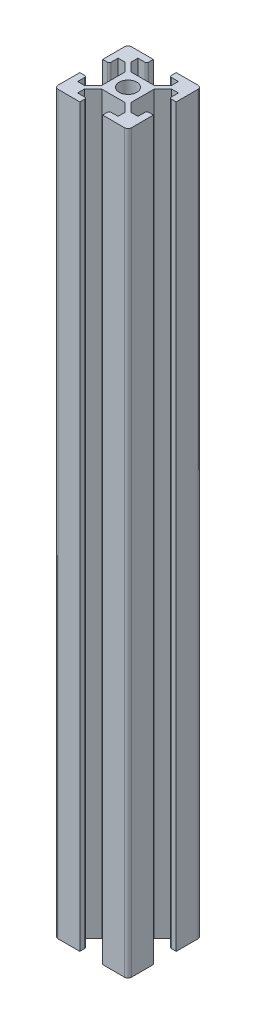
SolidWorks part; units mm, degrees
material "6063-T1"
ref_plane "Front Plane" through (0, 0, 0) normal (0, 0, 1) x (1, 0, 0)
ref_plane "Top Plane" through (0, 0, 0) normal (0, 1, 0) x (1, 0, 0)
ref_plane "Right Plane" through (0, 0, 0) normal (1, 0, 0) x (0, 0, -1)
sketch "Sketch1" plane through (0, 0, 0) normal (0, 1, 0) x (1, 0, 0)
  line L0 (0, 14.3976) -> (0, -18.4644) construction
  line L1 (-9, -10) -> (9, -10)
  line L2 (-10, -9) -> (-10, 9)
  line L3 (-9, 10) -> (9, 10)
  line L4 (10, -9) -> (10, 9)
  line L5 (-15.9976, 0) -> (13.6764, 0) construction
  line L6 (3.1, 10) -> (3.1, 8.2) construction
  line L7 (3.1, 8.2) -> (5.5, 8.2) construction
  line L8 (8.2, 5.5) -> (6.3765, 5.5) construction
  line L9 (3.1235, 4) -> (0, 4) construction
  line L10 (10, 3.1) -> (8.2, 3.1) construction
  line L11 (8.2, 3.1) -> (8.2, 5.5) construction
  line L12 (5.5, 8.2) -> (5.5, 6.3765) construction
  line L13 (4, 3.1235) -> (4, 0) construction
  line L14 (6.3765, 5.5) -> (4, 3.1235) construction
  line L15 (3.1, 10) -> (3.1, 8.7)
  line L16 (5.5, 6.3765) -> (3.1235, 4) construction
  line L17 (3.6, 8.2) -> (5.5, 8.2)
  line L18 (5.5, 8.2) -> (5.5, 6.3765)
  line L19 (5.5, 6.3765) -> (3.1235, 4)
  line L20 (3.1235, 4) -> (0, 4)
  line L21 (10, 3.1) -> (8.7, 3.1)
  line L22 (8.2, 3.6) -> (8.2, 5.5)
  line L23 (8.2, 5.5) -> (6.3765, 5.5)
  line L24 (6.3765, 5.5) -> (4, 3.1235)
  line L25 (4, 3.1235) -> (4, 0)
  line L26 (3.1, 10) -> (9, 10)
  line L27 (8.2, -5.5) -> (6.3765, -5.5)
  line L28 (8.2, -3.6) -> (8.2, -5.5)
  line L29 (10, -3.1) -> (8.7, -3.1)
  line L30 (6.3765, -5.5) -> (4, -3.1235)
  line L31 (4, -3.1235) -> (4, 0)
  line L32 (5.5, -6.3765) -> (3.1235, -4)
  line L33 (3.1235, -4) -> (0, -4)
  line L34 (5.5, -8.2) -> (5.5, -6.3765)
  line L35 (3.6, -8.2) -> (5.5, -8.2)
  line L36 (3.1, -10) -> (3.1, -8.7)
  line L37 (-5.5, -8.2) -> (-5.5, -6.3765)
  line L38 (-3.6, -8.2) -> (-5.5, -8.2)
  line L39 (-3.1, -10) -> (-3.1, -8.7)
  line L40 (-5.5, -6.3765) -> (-3.1235, -4)
  line L41 (-3.1235, -4) -> (0, -4)
  line L42 (-6.3765, -5.5) -> (-4, -3.1235)
  line L43 (-4, -3.1235) -> (-4, 0)
  line L44 (-8.2, -5.5) -> (-6.3765, -5.5)
  line L45 (-8.2, -3.6) -> (-8.2, -5.5)
  line L46 (-10, -3.1) -> (-8.7, -3.1)
  line L47 (-8.2, 5.5) -> (-6.3765, 5.5)
  line L48 (-8.2, 3.6) -> (-8.2, 5.5)
  line L49 (-10, 3.1) -> (-8.7, 3.1)
  line L50 (-6.3765, 5.5) -> (-4, 3.1235)
  line L51 (-4, 3.1235) -> (-4, 0)
  line L52 (-5.5, 6.3765) -> (-3.1235, 4)
  line L53 (-3.1235, 4) -> (0, 4)
  line L54 (-5.5, 8.2) -> (-5.5, 6.3765)
  line L55 (-3.6, 8.2) -> (-5.5, 8.2)
  line L56 (-3.1, 10) -> (-3.1, 8.7)
  circle A0 centre (0, 0) radius 2.4
  arc A1 (9, 10) -> (10, 9) centre (9, 9) cw
  arc A2 (9, -10) -> (10, -9) centre (9, -9) ccw
  arc A3 (-9, -10) -> (-10, -9) centre (-9, -9) cw
  arc A4 (-10, 9) -> (-9, 10) centre (-9, 9) cw
  arc A5 (8.7, 3.1) -> (8.2, 3.6) centre (8.7, 3.6) cw
  arc A6 (3.1, 8.7) -> (3.6, 8.2) centre (3.6, 8.7) ccw
  arc A7 (8.7, -3.1) -> (8.2, -3.6) centre (8.7, -3.6) ccw
  arc A8 (3.1, -8.7) -> (3.6, -8.2) centre (3.6, -8.7) cw
  arc A9 (-3.1, -8.7) -> (-3.6, -8.2) centre (-3.6, -8.7) ccw
  arc A10 (-8.7, -3.1) -> (-8.2, -3.6) centre (-8.7, -3.6) cw
  arc A11 (-8.7, 3.1) -> (-8.2, 3.6) centre (-8.7, 3.6) ccw
  arc A12 (-3.1, 8.7) -> (-3.6, 8.2) centre (-3.6, 8.7) cw
  point P0 (0, 0)
  point P10 (10, 10)
  point P13 (10, -10)
  point P18 (-10, 10)
  point P92 (0, 0)
  dimension "D5" = 4.8
  dimension "D6" = 1
  dimension "D17" = 0.5
  dimension "D1" = 20
  dimension "D2" = 20
  dimension "D3" = 10
  dimension "D4" = 10
  dimension "D7" = 1.8
  dimension "D8" = 1.8
  dimension "D9" = 3.1
  dimension "D10" = 3.1
  dimension "D11" = 5.5
  dimension "D12" = 4
  dimension "D13" = 5.5
  dimension "D14" = 4
  dimension "D15" = 4.2
  dimension "D16" = 45
  dimension "D18" = 3.1235
  dimension "D19" = 4
extrude "Boss-Extrude1" add sketch "Sketch1" along normal blind 200 contours A12 L56 L3 A4 L2 L49 A11 L48 L47 L50 L51 L43 L42 L44 L45 A10 L46 A3 L1 L39 A9 L38 L37 L40 L41 L33 L32 L34 L35 A8 L36 A2 L4 L29 A7 L28 L27 L30 L31 L25 L24 L23 L22 A5 L21 A1 L15
